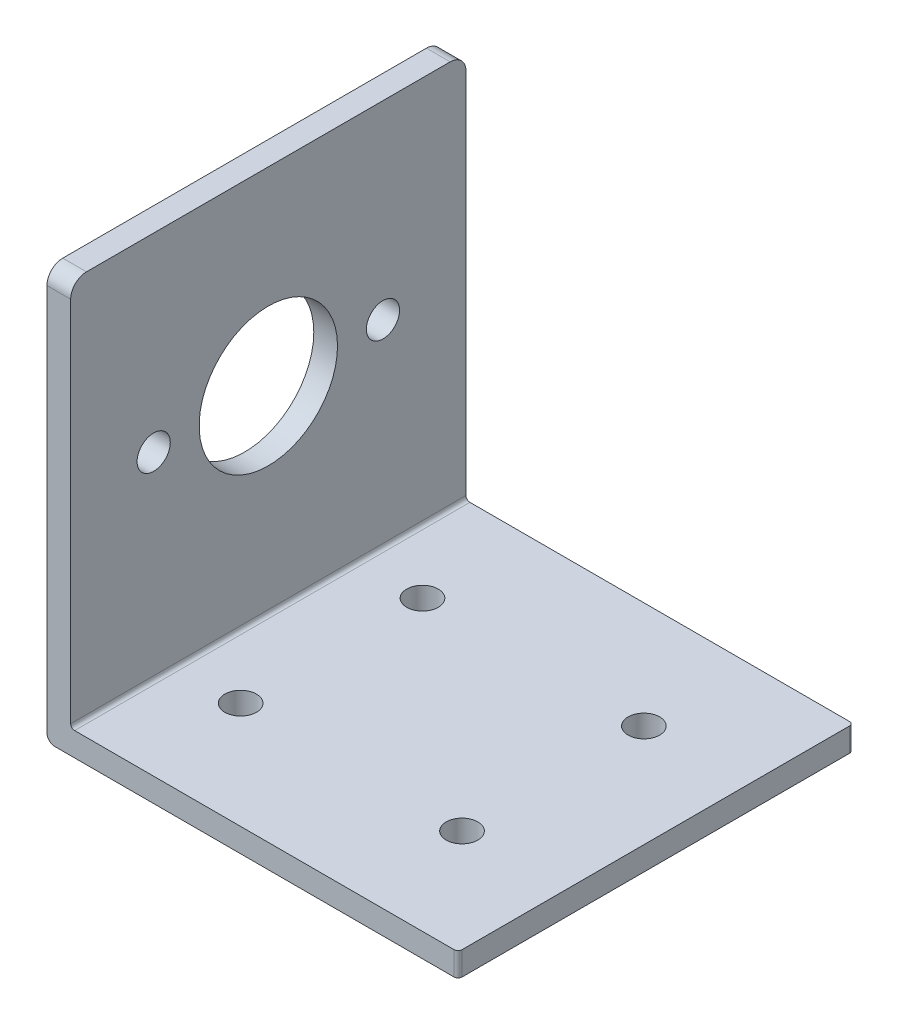
SolidWorks part; units mm, degrees
ref_plane "Front Plane" through (0, 0, 0) normal (0, 0, 1) x (1, 0, 0)
ref_plane "Top Plane" through (0, 0, 0) normal (0, 1, 0) x (1, 0, 0)
ref_plane "Right Plane" through (0, 0, 0) normal (1, 0, 0) x (0, 0, -1)
sketch "Sketch1" plane through (0, 0, 0) normal (0, 0, 1) x (1, 0, 0)
  line L0 (0, 0) -> (0, 49)
  line L1 (-3, 49) -> (-3, -2)
  line L2 (-2, -3) -> (49, -3)
  line L3 (49, 0) -> (0, 0)
  line L4 (-3, 49) -> (0, 49)
  line L5 (49, -3) -> (49, 0)
  arc A0 (-3, -2) -> (-2, -3) centre (-2, -2) ccw
  point P9 (-3, -3)
  dimension "D1" = 3
  dimension "D4" = 1
  dimension "D2" = 52
  dimension "D3" = 52
  dimension "D5" = 3
extrude "Boss-Extrude1" add sketch "Sketch1" along normal blind 50 contours L0 L4 L1 A0 L2 L5 L3
sketch "Sketch2" plane through (0, 0, 0) normal (1, 0, 0) x (0, 0, -1)
  line L0 (-25, 49) -> (-25, 0) construction
  line L1 (-50, 49) -> (0, 49) construction
  line L2 (-50, 0) -> (0, 0) construction
  line L3 (-50, -3) -> (0, -3) construction
  line L4 (0, 0) -> (0, 49) construction
  line L5 (0, 24.5) -> (-50, 24.5) construction
  line L6 (-50, 0) -> (-50, 49) construction
  line L7 (0, 49) -> (0, -2) construction
  circle A0 centre (-25, 25) radius 8.75
  circle A1 centre (-10.5, 25) radius 2.1
  circle A2 centre (-39.5, 25) radius 2.1
  dimension "D1" = 17.5
  dimension "D2" = 4.2
  dimension "D3" = 4.2
  dimension "D4" = 28
  dimension "D5" = 28
  dimension "D6" = 28
  dimension "D7" = 29
  dimension "D8" = 25
  dimension "D9" = 14.5
extrude "Cut-Extrude1" cut sketch "Sketch2" against normal blind 10
fillet "Fillet1" radius 2 2 edges at (-1.5, 49, 0) (-1.5, 49, 50)
fillet "Fillet2" radius 0.5 1 edges at (0, 0, 25)
fillet "Fillet3" radius 0.5 2 edges at (49, -1.5, 0) (49, -1.5, 50)
hole_wizard "Hole for M4 300® SC Nuts (SP)1" positions "Sketch3" profile "Sketch4" hole size "M4x0.7" standard "PEM® Metric" end condition through all
sketch "Sketch3" plane through (0, 0, 0) normal (0, 1, 0) x (1, 0, 0)
  line L0 (-2, 0) -> (48.5, 0) construction
  line L1 (-2, -50) -> (48.5, -50) construction
  line L3 (-3, -50) -> (-3, 0) construction
  point P0 (36, -13.5)
  point P2 (8, -13.5)
  point P4 (36, -36.5)
  point P6 (8, -36.5)
  point P9 (0, 0)
  point P14 (0, 0)
  dimension "D1" = 13.5
  dimension "D2" = 13.5
  dimension "D3" = 13.5
  dimension "D4" = 13.5
  dimension "D5" = 11
  dimension "D6" = 11
  dimension "D7" = 28
  dimension "D8" = 28
sketch "Sketch4" plane through (36, 0, 13.5) normal (1, 0, 0) x (0, 0, 1)
  line L0 (0, 0) -> (0, 3)
  line L1 (0, 3) -> (2, 3)
  line L2 (2, 3) -> (2, 0)
  line L5 (2, 0) -> (0, 0)
  line L11 (0, -6.35) -> (0, 107.95) construction
  dimension "Thru Hole Dia." = 4
  dimension "Thru Hole Depth" = 3
